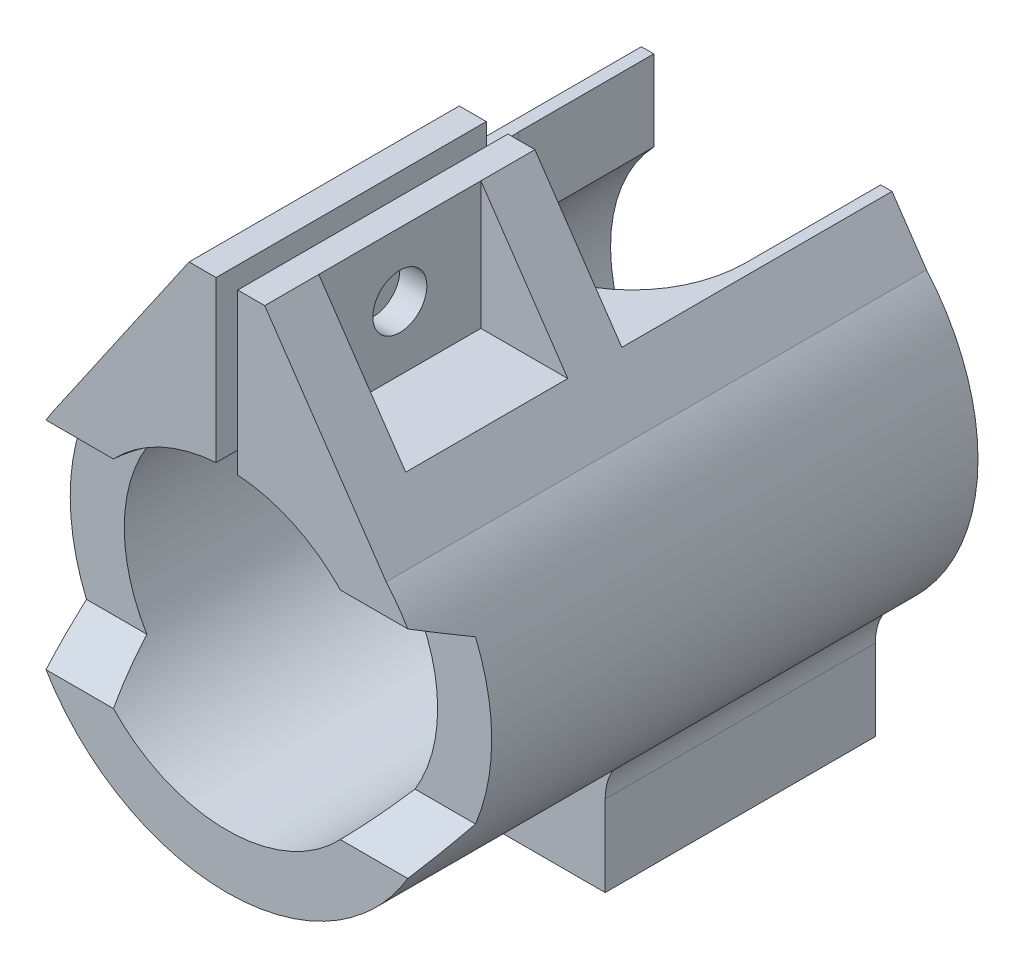
SolidWorks part; units mm, degrees
material "ABS"
ref_plane "Front Plane" through (0, 0, 0) normal (0, 0, 1) x (1, 0, 0)
ref_plane "Top Plane" through (0, 0, 0) normal (0, 1, 0) x (1, 0, 0)
ref_plane "Right Plane" through (0, 0, 0) normal (1, 0, 0) x (0, 0, -1)
sketch "Sketch1" plane through (0, 0, 0) normal (0, 0, 1) x (1, 0, 0)
  line L0 (0, 29.2916) -> (0, 14.5) construction
  line L1 (1, 29.2916) -> (1, 14.4655)
  line L2 (-1, 29.2916) -> (-1, 14.4655)
  line L4 (0, -55) -> (0, 55) construction
  line L6 (-3.5, 29.2916) -> (-16.0582, 11.0628)
  line L7 (3.5, 29.2916) -> (14.7337, 12.7738)
  line L8 (10, -19.5) -> (10, -27.5)
  line L9 (10, -27.5) -> (-10, -27.5)
  line L10 (-3.5, 29.2916) -> (-1, 29.2916)
  line L11 (1, 44.1585) -> (1, -43.2542) construction
  line L12 (1, 29.2916) -> (3.5, 29.2916)
  line L13 (0, 44.1585) -> (0, -43.2542) construction
  line L14 (0, -14.5) -> (0, -19.5) construction
  line L15 (-1, 44.1585) -> (-1, -43.2542) construction
  line L16 (-10, -19.5) -> (-10, -27.5)
  arc A0 (-1, 14.4655) -> (1, 14.4655) centre (0, 0) ccw
  arc A1 (19.5, 0) -> (14.7337, 12.7738) centre (0, 0) ccw
  arc A2 (0, -19.5) -> (19.5, 0) centre (0, 0) ccw
  arc A3 (10, -19.5) -> (12.4557, -15.0035) centre (15.3445, -19.5) cw
  arc A4 (-16.0582, 11.0628) -> (0, -19.5) centre (0, 0) ccw
  arc A5 (-10, -19.5) -> (-11.754, -15.5593) centre (-15.3036, -19.5) ccw
  dimension "D1" = 29
  dimension "D2" = 10
  dimension "D5" = 20
  dimension "D6" = 8
  dimension "D3" = 1
  dimension "D4" = 1
extrude "Boss-Extrude1" add sketch "Sketch1" against normal blind 50 contours L6 A4 A2 A3 A1 L7 L12 L1 A0 L2 L10 | A5 L16 L9 L8 A3 A2 A4
ref_plane "Plane1" through (14.5, 0, 0) normal (1, 0, 0) x (0, 0, -1)
ref_plane "Plane2" through (3.5, 0, 0) normal (1, 0, 0) x (0, 0, -1)
sketch "Sketch4" plane through (3.5, 0, 0) normal (1, 0, 0) x (0, 0, -1)
  line L5 (20, 29.2916) -> (20, 17.4655)
  line L11 (5, 29.2916) -> (5, 17.4655)
  line L13 (5, 29.2916) -> (5, 12.7738) construction
  line L14 (20, 29.2916) -> (20, 12.7738) construction
  line L15 (20, 17.4655) -> (5, 17.4655)
  line L19 (5, 29.2916) -> (20, 29.2916)
  dimension "D4" = 15
extrude "Cut-Extrude3" cut sketch "Sketch4" along normal through all
mirror "Mirror1" about plane through (0, 0, 0) normal (1, 0, 0) of "Cut-Extrude3"
sketch "Sketch5" plane through (3.5, 0, 0) normal (1, 0, 0) x (0, 0, -1)
  line L0 (12.5, 29.2916) -> (12.5, 17.4655) construction
  line L1 (20, 29.2916) -> (5, 29.2916) construction
  line L2 (20, 17.4655) -> (5, 17.4655) construction
  circle A1 centre (12.5, 23.3786) radius 2.5
extrude "Cut-Extrude4" cut sketch "Sketch5" against normal through all and the other way through all
ref_plane "Plane4" through (0, 14.5, 0) normal (0, 1, 0) x (1, 0, 0)
sketch "Sketch8" plane through (0, 14.5, 0) normal (0, 1, 0) x (1, 0, 0)
  line L0 (0, 52.4118) -> (0, -2.548) construction
  line L1 (0, -27.5) -> (0, 27.5) construction
  line L2 (-19.5, 50) -> (-1, 50) construction
  line L3 (-19.5, 37.5) -> (19.5, 37.5) construction
  line L4 (-10.5, 37.5) -> (-10.5, 50)
  line L5 (-10.5, 50) -> (-1, 50)
  line L6 (10.5, 50) -> (10.5, 37.5)
  line L7 (-1, 50) -> (-1, 27.0477)
  line L8 (1, 50) -> (1, 27.0477)
  line L9 (1, 50) -> (1, 0) construction
  line L10 (1, 50) -> (19.5, 50) construction
  line L11 (-19.5, 50) -> (19.5, 50) construction
  line L12 (1, 50) -> (10.5, 50)
  arc A0 (-10.5, 37.5) -> (-1, 27.0477) centre (0, 37.5) ccw
  arc A1 (1, 27.0477) -> (10.5, 37.5) centre (0, 37.5) ccw
  dimension "D1" = 12.5
sketch "Sketch9" plane through (3.5, 0, 0) normal (1, 0, 0) x (0, 0, -1)
  line L0 (5, 17.4655) -> (50, 17.4655) construction
  line L1 (50, 29.2916) -> (50, 11.0628) construction
  line L3 (25, 29.2916) -> (50, 29.2916)
  line L4 (25, 17.4655) -> (25, 29.2916)
  line L5 (25, 17.4655) -> (25, 29.2916)
  line L6 (50, 29.2916) -> (50, 17.4655)
  line L7 (50, 17.4655) -> (25, 17.4655)
  dimension "D1" = 5
extrude "Cut-Extrude8" cut sketch "Sketch9" against normal through all and the other way through all
extrude "Cut-Extrude9" cut sketch "Sketch8" against normal up to surface and the other way up to next up to face at (0, -0.0173, -25)
ref_plane "Plane5" through (0, 0, -37.5) normal (0, 0, 1) x (1, 0, 0)
sketch "Sketch10" plane through (0, 0, -37.5) normal (0, 0, 1) x (1, 0, 0)
  line L0 (0, 14.5) -> (0, -22.2883) construction
  line L1 (21.45, 14.5) -> (-21.45, 14.5) construction
  line L2 (0, -27.5) -> (0, 27.5) construction
  line L3 (-7, -12.6984) -> (7, -12.6984)
  line L5 (-7, -12.6984) -> (-7, -14.9416)
  line L7 (7, -12.6984) -> (7, -14.9416)
  arc A3 (-1.1379, 16.4607) -> (1.1379, 16.4607) centre (0, 0) ccw
  arc A4 (-7, -14.9416) -> (7, -14.9416) centre (0, 0) ccw
  dimension "D1" = 2
extrude "Cut-Extrude10" cut sketch "Sketch10" against normal through all and the other way blind 13
sketch "Sketch11" plane through (0, 0, 0) normal (1, 0, 0) x (0, 0, -1)
  line L0 (-2.5449, 0) -> (0, 0) construction
  line L1 (21.45, 0) -> (-21.45, 0) construction
  line L2 (-2.5449, -10) -> (0, -10) construction
  line L7 (-2.5449, 10) -> (0, 10) construction
  line L8 (0, 10) -> (0, -10)
  line L9 (0, 21.45) -> (0, -21.45) construction
  line L10 (5, 7.5) -> (5, -7.5)
  line L11 (-2.5449, -7.5) -> (5, -7.5) construction
  line L13 (-2.5449, 7.5) -> (5, 7.5) construction
  line L14 (0, 10) -> (5, 7.5)
  line L15 (5, -7.5) -> (0, -10)
  line L16 (-2.5449, -7.5) -> (52.5147, -7.5) construction
  line L17 (-2.5449, 10) -> (52.5147, 10) construction
  line L18 (5, 10) -> (5, -10) construction
  line L19 (-2.5449, 7.5) -> (52.5147, 7.5) construction
  line L21 (-2.5449, -10) -> (52.5147, -10) construction
  line L22 (5, 0) -> (52.5147, 0) construction
  line L23 (-2.5449, 0) -> (52.5147, 0) construction
  line L24 (5, 0) -> (52.5147, 0)
  dimension "D1" = 10
  dimension "D2" = 10
  dimension "D3" = 5
  dimension "D4" = 7.5
  dimension "D5" = 7.5
extrude "Cut-Extrude11" cut sketch "Sketch11" against normal through all and the other way through all contours L15 L10 L14 L8
sketch "Sketch13" plane through (0, -27.5, 0) normal (0, -1, 0) x (1, 0, 0)
  line L0 (4.106, -37.5) -> (-4.106, -37.5) construction
  line L1 (0, -31.0842) -> (-5.5563, -34.2921)
  line L2 (-5.5563, -34.2921) -> (-5.5563, -40.7079)
  line L3 (-5.5563, -40.7079) -> (0, -43.9158)
  line L4 (0, -43.9158) -> (5.5563, -40.7079)
  line L5 (5.5563, -40.7079) -> (5.5563, -34.2921)
  line L6 (5.5563, -34.2921) -> (0, -31.0842)
  line L7 (0, -27.5) -> (0, 27.5) construction
  circle A0 centre (0, -37.5) radius 5.5563 construction
extrude "Cut-Extrude15" cut sketch "Sketch13" against normal up to next
sketch "Sketch14" plane through (0, -27.5, 0) normal (0, -1, 0) x (1, 0, 0)
  line L1 (5.5563, -40.7079) -> (5.5562, -34.2921)
  line L2 (5.5562, -34.2921) -> (0, -31.0842)
  line L3 (0, -31.0842) -> (-5.5563, -34.2921)
  line L4 (-5.5563, -34.2921) -> (-5.5562, -40.7079)
  line L5 (-5.5562, -40.7079) -> (0, -43.9158)
  line L6 (0, -43.9158) -> (5.5563, -40.7079)
  circle A0 centre (0, -37.5) radius 5.5563 construction
  circle A1 centre (0, -37.5) radius 3.375
extrude "Boss-Extrude2" add sketch "Sketch14" against normal blind 2.5
sketch "Sketch15" plane through (0, 0, 0) normal (0, 0, 1) x (1, 0, 0)
  line L0 (-19.5, 0) -> (-19.5, -27.5)
  line L1 (-19.5, -27.5) -> (19.5, -27.5)
  line L2 (19.5, -27.5) -> (19.5, 0)
  arc A0 (-19.5, 0) -> (19.5, 0) centre (0, 0) ccw
extrude "Cut-Extrude17" cut sketch "Sketch15" against normal blind 25
sketch "Sketch16" plane through (0, -27.5, 0) normal (0, -1, 0) x (1, 0, 0)
  line L1 (-10, -25) -> (10, -25)
  line L2 (-10, -25) -> (-10, -50)
  line L3 (-10, -50) -> (10, -50)
  line L4 (10, -25) -> (10, -50)
extrude "Cut-Extrude18" cut sketch "Sketch16" against normal blind 0.5
